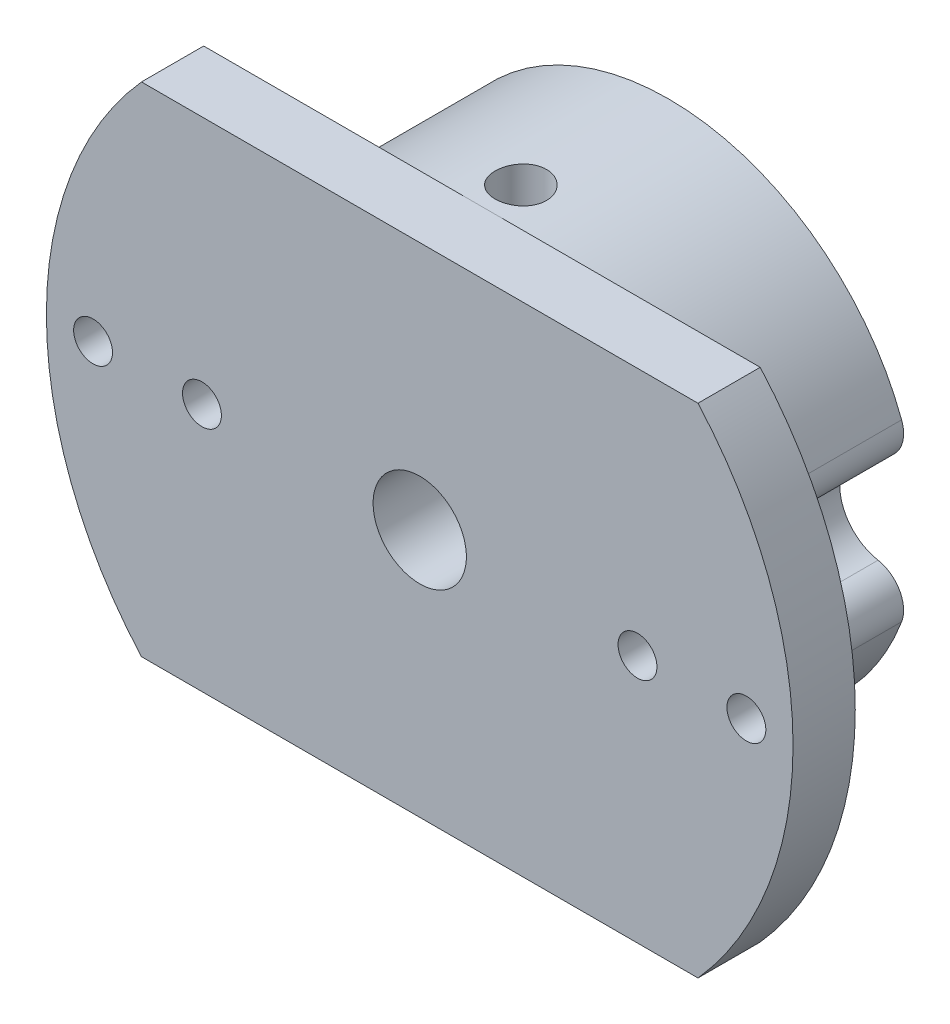
SolidWorks part; units mm, degrees
ref_plane "Front Plane" through (0, 0, 0) normal (0, 0, 1) x (1, 0, 0)
ref_plane "Top Plane" through (0, 0, 0) normal (0, 1, 0) x (1, 0, 0)
ref_plane "Right Plane" through (0, 0, 0) normal (1, 0, 0) x (0, 0, -1)
ref_plane "Plane1" through (0, 0, 12) normal (0, 0, -1) x (-1, 0, 0)
sketch "Sketch1" plane through (0, 0, 12) normal (0, 0, -1) x (-1, 0, 0)
  line L0 (-17.8885, -16) -> (17.8885, -16)
  line L1 (17.8885, 16) -> (-17.8885, 16)
  arc A0 (17.8885, -16) -> (17.8885, 16) centre (0, 0) ccw
  arc A1 (-17.8885, 16) -> (-17.8885, -16) centre (0, 0) ccw
extrude "Boss-Extrude1" add sketch "Sketch1" against normal blind 4
ref_plane "Plane2" through (0, 0, 12) normal (0, 0, 1) x (1, 0, 0)
ref_plane "Plane3" through (0, 0, 0) normal (0, 0, -1) x (-1, 0, 0)
sketch "Sketch3" plane through (0, 0, 0) normal (0, 0, -1) x (-1, 0, 0)
  arc A0 (-15.8214, 2.3838) -> (-15.8214, -2.3838) centre (-14, 0) cw
  arc A1 (-15.8214, -2.3838) -> (15.8214, -2.3838) centre (0, 0) ccw
  arc A2 (15.8214, -2.3838) -> (15.8214, 2.3838) centre (14, 0) cw
  arc A3 (15.8214, 2.3838) -> (-15.8214, 2.3838) centre (0, 0) ccw
extrude "Boss-Extrude2" add sketch "Sketch3" against normal up to surface up to plane "Plane2"
hole_wizard "#2 Clearance Hole1" positions "Sketch5" profile "Sketch4" hole size "#2" standard "ANSI Inch"
sketch "Sketch5" plane through (0, 0, 12) normal (0, 0, -1) x (-1, 0, 0)
  point P0 (21, 0)
  point P1 (-21, 0)
  point P2 (-14, 0)
  point P3 (14, 0)
sketch "Sketch4" plane through (-21, 0, 12) normal (1, 0, 0) x (0, 1, 0)
  line L0 (0, 0) -> (0, 4)
  line L1 (0, 4) -> (1.25, 4)
  line L2 (1.25, 4) -> (1.25, 0)
  line L5 (1.25, 0) -> (0, 0)
  line L11 (0, -6.35) -> (0, 107.95) construction
  dimension "Thru Hole Dia." = 2.5
  dimension "Thru Hole Depth" = 4
hole_wizard "#12 Clearance Hole1" positions "Sketch7" profile "Sketch6" hole size "#12" standard "ANSI Inch"
sketch "Sketch7" plane through (0, 0, 0) normal (0, 0, -1) x (-1, 0, 0)
  point P0 (0, 0)
sketch "Sketch6" plane through (0, 0, 0) normal (1, 0, 0) x (0, 1, 0)
  line L0 (0, 0) -> (0, 16)
  line L1 (0, 16) -> (3, 16)
  line L2 (3, 16) -> (3, 0)
  line L5 (3, 0) -> (0, 0)
  line L11 (0, -6.35) -> (0, 107.95) construction
  dimension "Thru Hole Dia." = 6
  dimension "Thru Hole Depth" = 16
hole_wizard "#4 Clearance Hole1" positions "3DSketch1" profile "Sketch8" hole size "#4" standard "ANSI Inch"
sketch3d "3DSketch1"
  point P0 (0, 16, 9.5)
sketch "Sketch8" plane through (0, 16, 9.5) normal (1, 0, 0) x (0, 0, 1)
  line L0 (0, 0) -> (0, 13)
  line L1 (0, 13) -> (1.65, 13)
  line L2 (1.65, 13) -> (1.65, 0)
  line L5 (1.65, 0) -> (0, 0)
  line L11 (0, -6.35) -> (0, 107.95) construction
  dimension "Thru Hole Dia." = 3.3
  dimension "Thru Hole Depth" = 13
ref_plane "Plane4" through (0, -2.5055, 0) normal (0, 1, 0) x (1, 0, 0)
hole_wizard "#4 Clearance Hole2" positions "Sketch10" profile "Sketch9" hole size "#4" standard "ANSI Inch"
sketch "Sketch10" plane through (0, -2.5055, 0) normal (0, 1, 0) x (1, 0, 0)
  point P0 (0, -3.5)
sketch "Sketch9" plane through (0, -2.5055, 3.5) normal (1, 0, 0) x (0, 0, 1)
  line L0 (0, 0) -> (0, 32)
  line L1 (0, 32) -> (1.65, 32)
  line L2 (1.65, 32) -> (1.65, 0)
  line L5 (1.65, 0) -> (0, 0)
  line L10 (0, 32) -> (-1.65, 32) construction
  line L11 (0, -6.35) -> (0, 107.95) construction
  dimension "Hole Dia." = 3.3
  dimension "Hole Depth" = 32
  dimension "Drill Angle" = 180
fillet "Fillet1" radius 2 4 edges at (-15.8214, 2.3838, 6) (-15.8214, -2.3838, 6) (15.8214, 2.3838, 6) (15.8214, -2.3838, 6)
